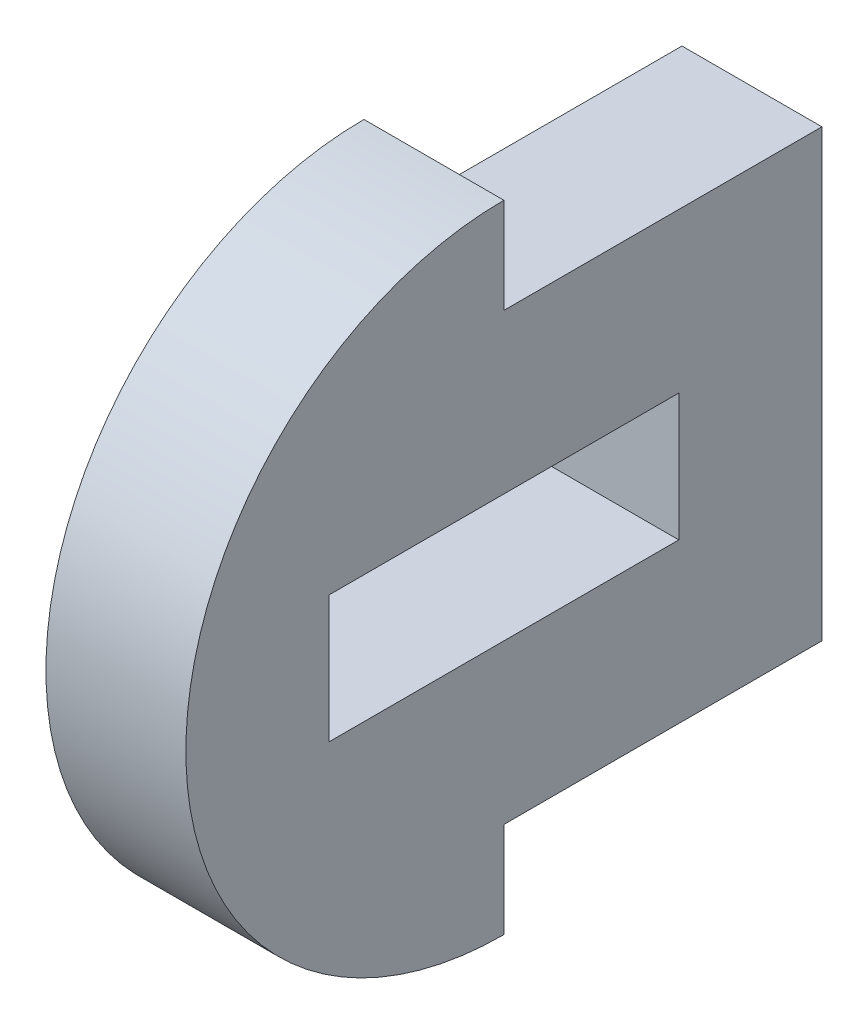
SolidWorks part; units mm, degrees
ref_plane "Front Plane" through (0, 0, 0) normal (0, 0, 1) x (1, 0, 0)
ref_plane "Top Plane" through (0, 0, 0) normal (0, 1, 0) x (1, 0, 0)
ref_plane "Right Plane" through (0, 0, 0) normal (1, 0, 0) x (0, 0, -1)
sketch "Sketch1" plane through (0, 0, 0) normal (1, 0, 0) x (0, 0, -1)
  line L0 (0, 10) -> (0, 7)
  line L1 (0, 7) -> (10, 7)
  line L2 (10, 7) -> (10, -7)
  line L3 (10, -7) -> (0, -7)
  line L4 (0, -7) -> (0, -10)
  line L6 (-5.5, 2) -> (5.5, 2)
  line L7 (-5.5, 2) -> (-5.5, -2)
  line L8 (-5.5, -2) -> (5.5, -2)
  line L9 (5.5, 2) -> (5.5, -2)
  arc A0 (0, 10) -> (0, -10) centre (0, 0) ccw
  dimension "D1" = 20
  dimension "D2" = 3
  dimension "D3" = 3
  dimension "D4" = 10
  dimension "D5" = 11
  dimension "D6" = 5.5
  dimension "D7" = 4
  dimension "D8" = 2
extrude "Boss-Extrude1" add sketch "Sketch1" along normal blind 4.4
equation "\"fit\"= 1"
equation "\"phone thick\"= 9.5"
equation "\"phone support width\"= 10"
equation "\"Thicker acrylic\"= 4.4"
equation "\"Thinner acrylic\" = 3"
equation "\"D4@Sketch1\"=10"
equation "\"D5@Sketch1\"=\"phone support width\"+\"fit\""
equation "\"D6@Sketch1\"=\"D5@Sketch1\"/2"
equation "\"D7@Sketch1\"=\"Thinner acrylic\"+\"fit\""
equation "\"D8@Sketch1\"=\"D7@Sketch1\"/2"
equation "\"Phone segment thick\"= 20"
equation "\"D1@Sketch1\"=\"Phone segment thick\""
equation "\"D2@Sketch1\"=\"Thinner acrylic\""
equation "\"D3@Sketch1\"=\"Thinner acrylic\""
